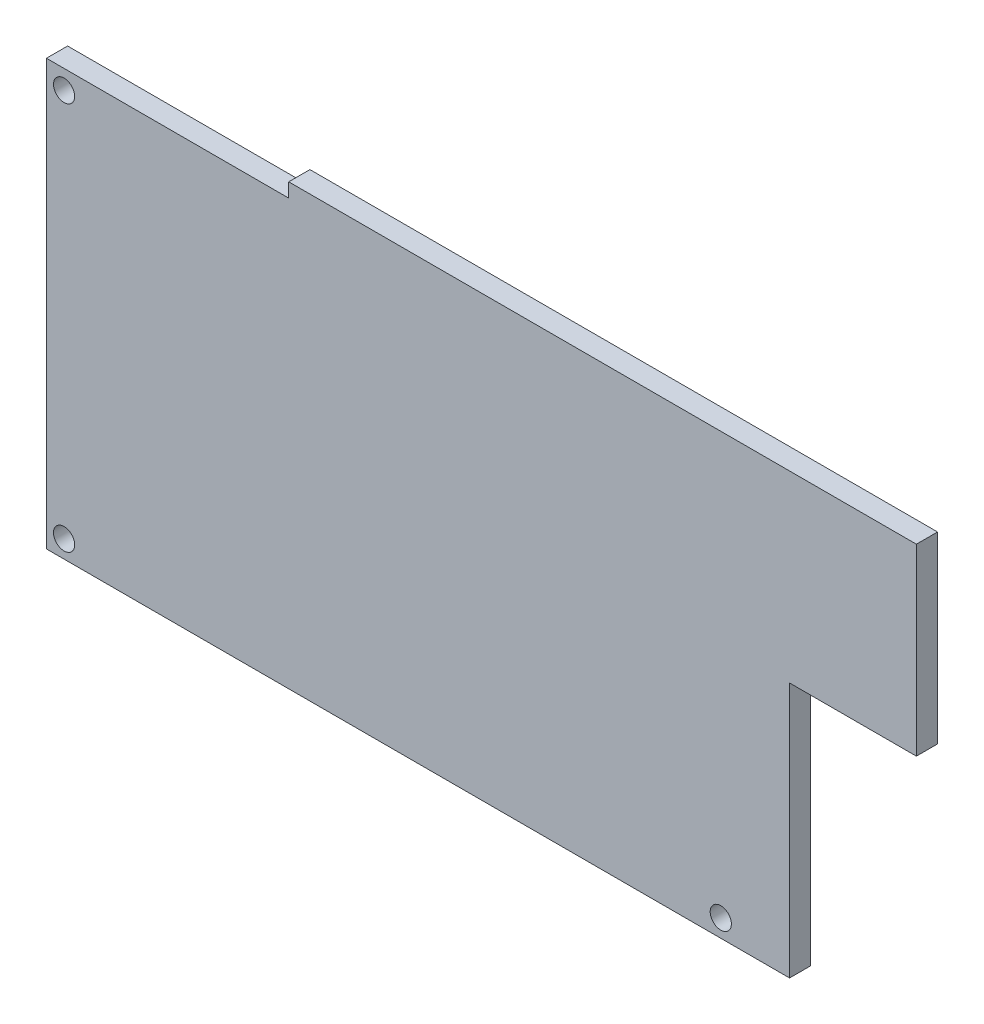
SolidWorks part; units mm, degrees
ref_plane "Front Plane" through (0, 0, 0) normal (0, 0, 1) x (1, 0, 0)
ref_plane "Top Plane" through (0, 0, 0) normal (0, 1, 0) x (1, 0, 0)
ref_plane "Right Plane" through (0, 0, 0) normal (1, 0, 0) x (0, 0, -1)
sketch "Sketch1" plane through (0, 0, 0) normal (0, 0, 1) x (1, 0, 0)
  line L0 (94.6769, -76.2293) -> (94.6769, -77.7741) construction
  line L1 (119.8774, -74.2293) -> (30.9908, -74.2293)
  line L2 (119.8774, -74.2293) -> (119.8774, -100.2293)
  line L3 (119.8774, -100.2293) -> (101.9182, -100.2293)
  line L4 (30.9908, -74.2293) -> (30.9908, -76.2293)
  line L5 (94.6769, -76.2293) -> (101.9182, -76.2293)
  line L6 (-3.3231, -76.2293) -> (30.9908, -76.2293)
  line L7 (-3.3231, -76.2293) -> (-3.3231, -136.4143)
  line L8 (-3.3231, -136.4143) -> (101.9182, -136.4143)
  line L9 (101.9182, -100.2293) -> (101.9182, -136.4143)
  line L11 (30.9908, -76.2293) -> (-3.3231, -76.2293)
  line L17 (109.9908, -130.9043) -> (109.9908, -80.9043)
  dimension "D7" = 24
  dimension "D8" = 2
extrude "Boss-Extrude1" add sketch "Sketch1" along normal blind 3
sketch "Sketch2" plane through (0, 0, 0) normal (0, 0, -1) x (-1, 0, 0)
  circle A0 centre (-92.1769, -133.9143) radius 1.5
  circle A1 centre (0.8231, -133.9143) radius 1.5
  circle A2 centre (0.8231, -78.9143) radius 1.5
extrude "Cut-Extrude1" cut sketch "Sketch2" against normal blind 10
sketch "Sketch3" plane through (0, 0, -5) normal (0, 0, -1) x (-1, 0, 0)
  line L0 (-92.1769, -133.9143) -> (-120.2861, -133.9143) construction
  line L1 (-120.2861, -133.9143) -> (-120.2861, -66.8061) construction
  line L2 (-92.1769, -78.9143) -> (-125.1438, -78.9143) construction
  line L3 (-123.1745, -66.8061) -> (-123.1745, -133.9143) construction
  circle A0 centre (-123.1745, -133.9143) radius 1.55
  circle A1 centre (-123.1745, -78.9143) radius 1.55
  dimension "D1" = 3.1
  dimension "D2" = 3.1
